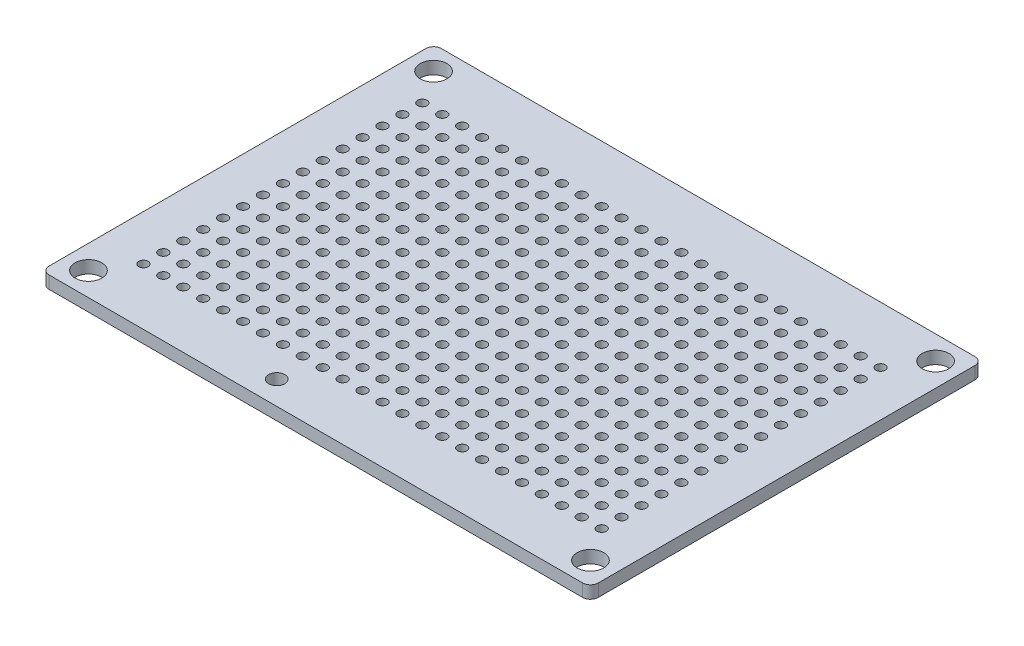
SolidWorks part; units mm, degrees
ref_plane "Front Plane" through (0, 0, 0) normal (0, 0, 1) x (1, 0, 0)
ref_plane "Top Plane" through (0, 0, 0) normal (0, 1, 0) x (1, 0, 0)
ref_plane "Right Plane" through (0, 0, 0) normal (1, 0, 0) x (0, 0, -1)
sketch "Sketch1" plane through (0, 0, 0) normal (0, 1, 0) x (1, 0, 0)
  line L1 (0, 0) -> (70, 0)
  line L2 (0, 0) -> (0, 50)
  line L3 (0, 50) -> (70, 50)
  line L4 (70, 0) -> (70, 50)
  dimension "D1" = 50
  dimension "D2" = 70
extrude "Boss-Extrude1" add sketch "Sketch1" along normal blind 1.6 contours L3 L4 L1 L2
fillet "Fillet1" radius 1 4 edges at (0, 0.8, -50) (70, 0.8, -50) (0, 0.8, 0) (70, 0.8, 0)
ref_plane "Plane1" through (0, 0, -25) normal (0, 0, -1) x (-1, 0, 0)
ref_plane "Plane2" through (35, 0, 0) normal (-1, 0, 0) x (0, 0, 1)
hole_wizard "M3 Clearance Hole1" positions "Sketch4" profile "Sketch5" hole size "M3" standard "ISO"
sketch "Sketch4" plane through (0, 1.6, 0) normal (0, 1, 0) x (1, 0, 0)
  line L0 (0, 1) -> (0, 49) construction
  line L1 (1, 0) -> (69, 0) construction
  point P0 (3, 3)
  dimension "D1" = 3
  dimension "D2" = 3
sketch "Sketch5" plane through (3, 1.6, -3) normal (1, 0, 0) x (0, 0, 1)
  line L0 (0, 0) -> (0, 5.0215)
  line L1 (0, 5.0215) -> (1.7, 4)
  line L2 (1.7, 4) -> (1.7, 0)
  line L5 (1.7, 0) -> (0, 0)
  line L10 (0, 5.0215) -> (-1.7, 4) construction
  line L11 (0, -6.35) -> (0, 107.95) construction
  dimension "Hole Dia." = 3.4
  dimension "Hole Depth" = 4
  dimension "Drill Angle" = 118
mirror "Mirror1" about plane through (0, 0, -25) normal (0, 0, -1) of "M3 Clearance Hole1"
mirror "Mirror2" about plane through (35, 0, 0) normal (-1, 0, 0) of "Mirror1", "M3 Clearance Hole1"
hole_wizard "M1 Clearance Hole1" positions "Sketch6" profile "Sketch7" hole size "M1" standard "ISO"
sketch "Sketch6" plane through (0, 1.6, 0) normal (0, 1, 0) x (1, 0, 0)
  line L1 (0, 1) -> (0, 49) construction
  point P0 (5.79, 25)
  dimension "D1" = 5.79
sketch "Sketch7" plane through (5.79, 1.6, -25) normal (1, 0, 0) x (0, 0, 1)
  line L0 (0, 0) -> (0, 4.3605)
  line L1 (0, 4.3605) -> (0.6, 4)
  line L2 (0.6, 4) -> (0.6, 0)
  line L5 (0.6, 0) -> (0, 0)
  line L10 (0, 4.3605) -> (-0.6, 4) construction
  line L11 (0, -6.35) -> (0, 107.95) construction
  dimension "Hole Dia." = 1.2
  dimension "Hole Depth" = 4
  dimension "Drill Angle" = 118
pattern_linear "LPattern1" count 24 spacing 2.54 along (1, 0, 0) of "M1 Clearance Hole1"
pattern_linear "LPattern2" count 8 spacing 2.54 along (0, 0, -1) count 8 spacing 2.54 along (0, 0, 1) of "LPattern1", "M1 Clearance Hole1"
hole_wizard "Tap Drill for M2.5x0.45 Tap1" positions "Sketch8" profile "Sketch9" hole size "M2.5x0.45" standard "ANSI Metric"
sketch "Sketch8" plane through (0, 1.6, 0) normal (0, 1, 0) x (1, 0, 0)
  circle A0 centre (67, 3) radius 1.7 construction
  point P0 (27, 3)
  dimension "D1" = 40
sketch "Sketch9" plane through (27, 1.6, -3) normal (1, 0, 0) x (0, 0, 1)
  line L0 (0, 0) -> (0, 38.7159)
  line L1 (0, 38.7159) -> (1.025, 38.1)
  line L2 (1.025, 38.1) -> (1.025, 0)
  line L5 (1.025, 0) -> (0, 0)
  line L10 (0, 38.7159) -> (-1.025, 38.1) construction
  line L11 (0, -6.35) -> (0, 107.95) construction
  dimension "Hole Dia." = 2.05
  dimension "Hole Depth" = 38.1
  dimension "Drill Angle" = 118
